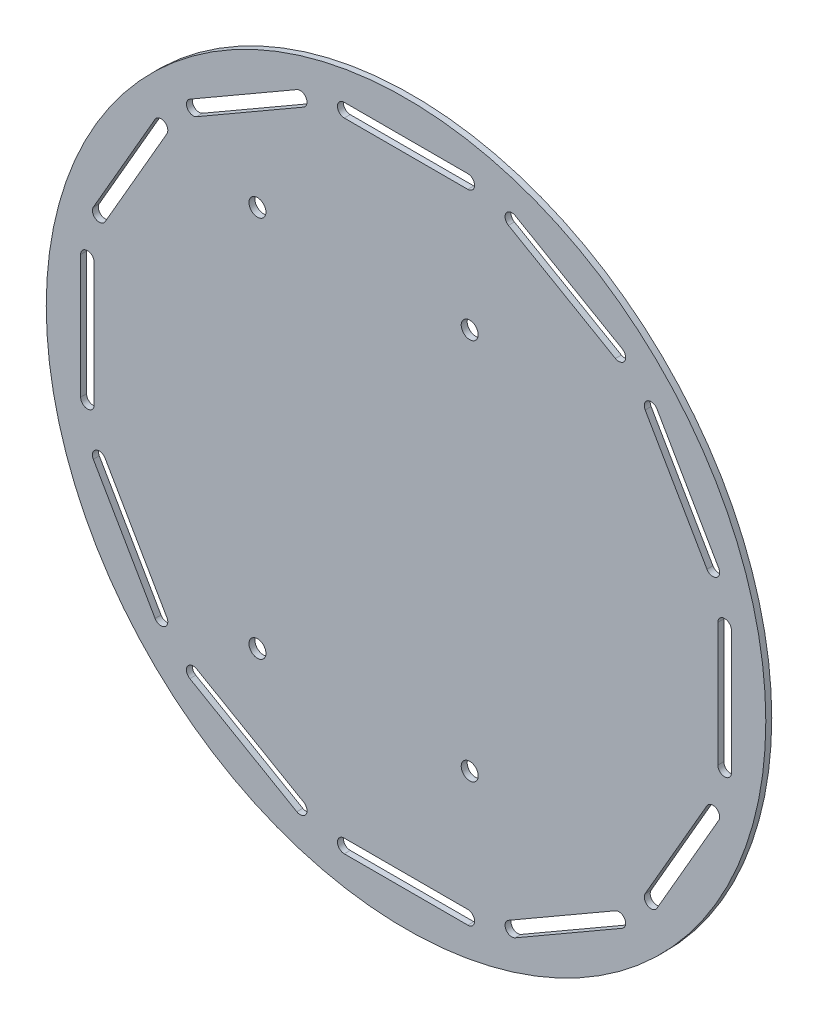
SolidWorks part; units mm, degrees
material "3.3535 (EN-AW 5754)"
ref_plane "Front" through (0, 0, 0) normal (0, 0, 1) x (1, 0, 0)
ref_plane "Top" through (0, 0, 0) normal (0, 1, 0) x (1, 0, 0)
ref_plane "Right" through (0, 0, 0) normal (1, 0, 0) x (0, 0, -1)
sketch "Эскиз1" plane through (0, 0, 0) normal (0, 0, 1) x (1, 0, 0)
  line L0 (0, 0) -> (0, 26.6616) construction
  line L1 (0, 0) -> (-24.5807, 0) construction
  line L2 (0, -45) -> (0, 45) construction
  line L3 (0, 45) -> (15, 45) construction
  line L4 (0, 45) -> (-35, 45) construction
  line L5 (0, -45) -> (-35, -45) construction
  line L6 (0, -45) -> (15, -45) construction
  line L7 (-35, 45) -> (-35, -45) construction
  circle A0 centre (0, 0) radius 84.75
  circle A2 centre (15, 45) radius 2
  circle A3 centre (-35, 45) radius 2
  circle A4 centre (-35, -45) radius 2
  circle A5 centre (15, -45) radius 2
  dimension "D1" = 169.5
  dimension "D2" = 50
  dimension "D3" = 35
  dimension "D4" = 50
  dimension "D5" = 15
extrude "Бобышка-Вытянуть1" add sketch "Эскиз1" along normal blind 1.4
sketch "Эскиз2" plane through (0, 0, 1.4) normal (0, 0, 1) x (1, 0, 0)
  line L0 (73.45, -14.55) -> (73.45, 14.55)
  line L2 (76.65, -14.55) -> (76.65, 14.55)
  line L3 (0, 0) -> (16.5568, 0) construction
  line L4 (0, 0) -> (0, 11.9695) construction
  line L6 (73.45, 0) -> (76.65, 0) construction
  line L7 (75.05, -14.55) -> (75.05, 14.55) construction
  circle A0 centre (0, 0) radius 76.65 construction
  circle A1 centre (0, 0) radius 73.45 construction
  arc A7 (76.65, 14.55) -> (73.45, 14.55) centre (75.05, 14.55) ccw
  arc A8 (76.65, -14.55) -> (73.45, -14.55) centre (75.05, -14.55) cw
  point P6 (75.05, 0)
  point P7 (73.45, 0)
  point P23 (76.65, 0)
  dimension "D3" = 153.3
  dimension "D4" = 146.9
extrude "Вырез-Вытянуть1" cut sketch "Эскиз2" against normal blind 1.4
pattern_circular "Круговой массив1" count 12 over 360 about axis through (0, 0, 0) along (0, 0, 1) of "Вырез-Вытянуть1"
sketch "Эскиз3" plane through (0, 0, 1.4) normal (0, 0, 1) x (1, 0, 0)
  circle A2 centre (75.05, 0) radius 1.6
  circle A4 centre (75.05, 14.55) radius 1.6
  circle A5 centre (75.05, -14.55) radius 1.6
  circle A8 centre (64.9952, -37.525) radius 1.6
  circle A9 centre (72.2702, -24.9243) radius 1.6
  circle A10 centre (57.7202, -50.1257) radius 1.6
  circle A11 centre (37.525, -64.9952) radius 1.6
  circle A12 centre (50.1257, -57.7202) radius 1.6
  circle A13 centre (24.9243, -72.2702) radius 1.6
  circle A14 centre (0, -75.05) radius 1.6
  circle A15 centre (14.55, -75.05) radius 1.6
  circle A16 centre (-14.55, -75.05) radius 1.6
  circle A17 centre (-37.525, -64.9952) radius 1.6
  circle A18 centre (-24.9243, -72.2702) radius 1.6
  circle A19 centre (-50.1257, -57.7202) radius 1.6
  circle A20 centre (-64.9952, -37.525) radius 1.6
  circle A21 centre (-57.7202, -50.1257) radius 1.6
  circle A22 centre (-72.2702, -24.9243) radius 1.6
  circle A23 centre (-75.05, 0) radius 1.6
  circle A24 centre (-75.05, -14.55) radius 1.6
  circle A25 centre (-75.05, 14.55) radius 1.6
  circle A26 centre (-64.9952, 37.525) radius 1.6
  circle A27 centre (-72.2702, 24.9243) radius 1.6
  circle A28 centre (-57.7202, 50.1257) radius 1.6
  circle A29 centre (-37.525, 64.9952) radius 1.6
  circle A30 centre (-50.1257, 57.7202) radius 1.6
  circle A31 centre (-24.9243, 72.2702) radius 1.6
  circle A32 centre (0, 75.05) radius 1.6
  circle A33 centre (-14.55, 75.05) radius 1.6
  circle A34 centre (14.55, 75.05) radius 1.6
  circle A35 centre (37.525, 64.9952) radius 1.6
  circle A36 centre (24.9243, 72.2702) radius 1.6
  circle A37 centre (50.1257, 57.7202) radius 1.6
  circle A38 centre (64.9952, 37.525) radius 1.6
  circle A39 centre (57.7202, 50.1257) radius 1.6
  circle A40 centre (72.2702, 24.9243) radius 1.6
  point P81 (0, 0)
